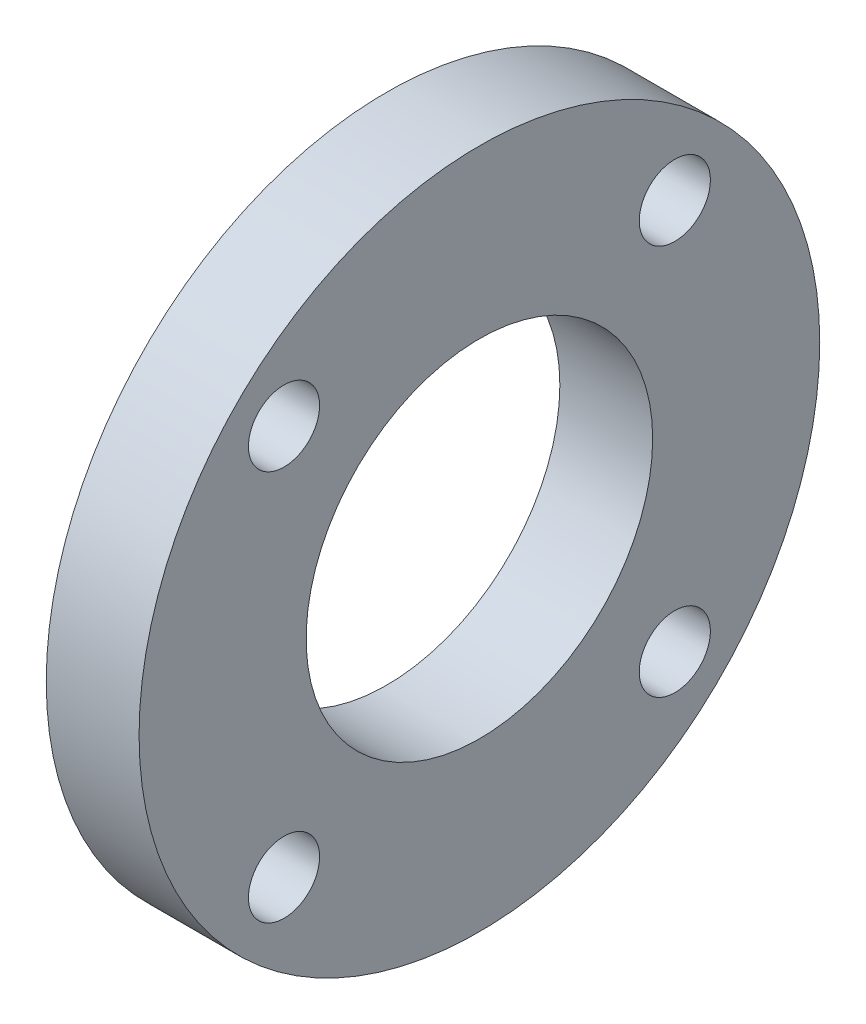
SolidWorks part; units mm, degrees
material "Alumina"
ref_plane "Front Plane" through (0, 0, 0) normal (0, 0, 1) x (1, 0, 0)
ref_plane "Top Plane" through (0, 0, 0) normal (0, 1, 0) x (1, 0, 0)
ref_plane "Right Plane" through (0, 0, 0) normal (1, 0, 0) x (0, 0, -1)
sketch "Sketch2" plane through (0, 0, 0) normal (1, 0, 0) x (0, 0, -1)
  circle A0 centre (0, 0) radius 11
  circle A1 centre (0, 0) radius 5.6
  dimension "D1" = 22
  dimension "D2" = 11.2
extrude "Boss-Extrude1" add sketch "Sketch2" along normal blind 3 separate body
sketch "Sketch3" plane through (0, 0, 0) normal (1, 0, 0) x (0, 0, -1)
  line L0 (0, 0) -> (0, 11) construction
  line L1 (0, 0) -> (11, 0) construction
  line L2 (0, 0) -> (7.7782, 7.7782) construction
  circle A0 centre (0, 0) radius 11 construction
  circle A1 centre (0, 0) radius 8.5 construction
  circle A2 centre (6.3155, 6.3155) radius 1.15
  circle A3 centre (6.3155, -6.3155) radius 1.15
  circle A4 centre (-6.3155, -6.3155) radius 1.15
  circle A5 centre (-6.3155, 6.3155) radius 1.15
  point P20 (0, 0)
  dimension "D2" = 17
  dimension "D3" = 2.3
  dimension "D1" = 45
  dimension "D4" = 4
extrude "Cut-Extrude1" cut sketch "Sketch3" along normal through all
